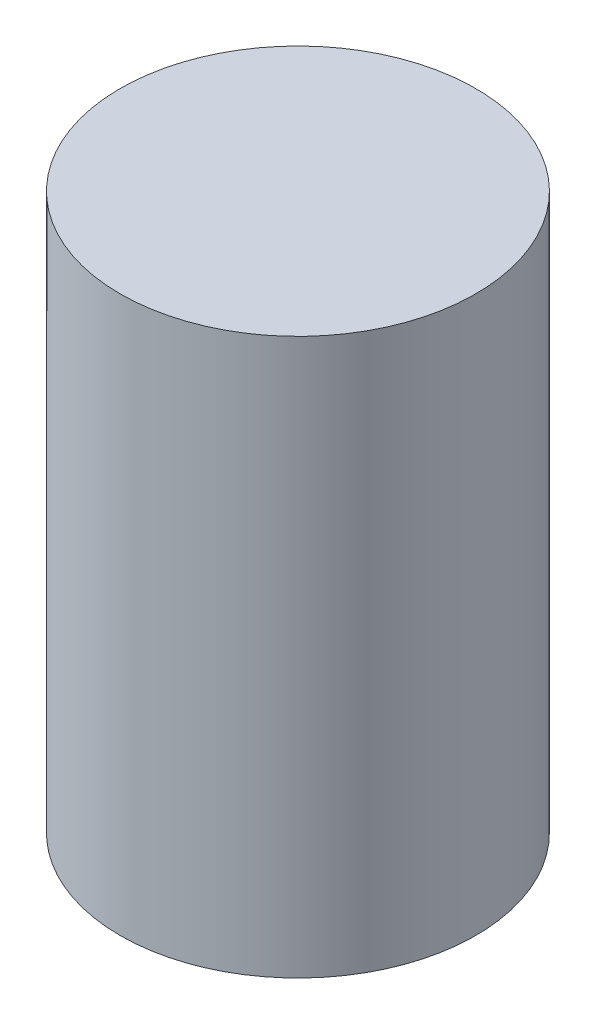
SolidWorks part; units mm, degrees
ref_plane "Alzado" through (0, 0, 0) normal (0, 0, 1) x (1, 0, 0)
ref_plane "Planta" through (0, 0, 0) normal (0, 1, 0) x (1, 0, 0)
ref_plane "Vista lateral" through (0, 0, 0) normal (1, 0, 0) x (0, 0, -1)
sketch "Sketch1" plane through (0, 0, 0) normal (0, 1, 0) x (1, 0, 0)
  circle A0 centre (0, 0) radius 4.8
  dimension "D1" = 9.6
extrude "Boss-Extrude1" add sketch "Sketch1" along normal blind 15
sketch "Sketch2" plane through (0, 0, 0) normal (1, 0, 0) x (0, 0, -1)
  line L0 (0, 18.0643) -> (0, -1.8562) construction
  line L1 (-2.5, 0) -> (2.5, 0)
  line L2 (-4.8, 0) -> (4.8, 0) construction
  line L3 (-2.5, 0) -> (-2.5, 4)
  line L4 (-2.5, 4) -> (-2, 4)
  line L5 (-2, 4) -> (-2, 8)
  line L6 (-2, 8) -> (2, 8)
  line L7 (2.5, 0) -> (2.5, 4)
  line L8 (2.5, 4) -> (2, 4)
  line L9 (2, 4) -> (2, 8)
  point P12 (0, 0)
  point P15 (0, 8)
  dimension "D1" = 2.5
  dimension "D2" = 8
  dimension "D3" = 4
  dimension "D4" = 4
extrude "Cut-Extrude1" cut sketch "Sketch2" against normal mid plane 2
